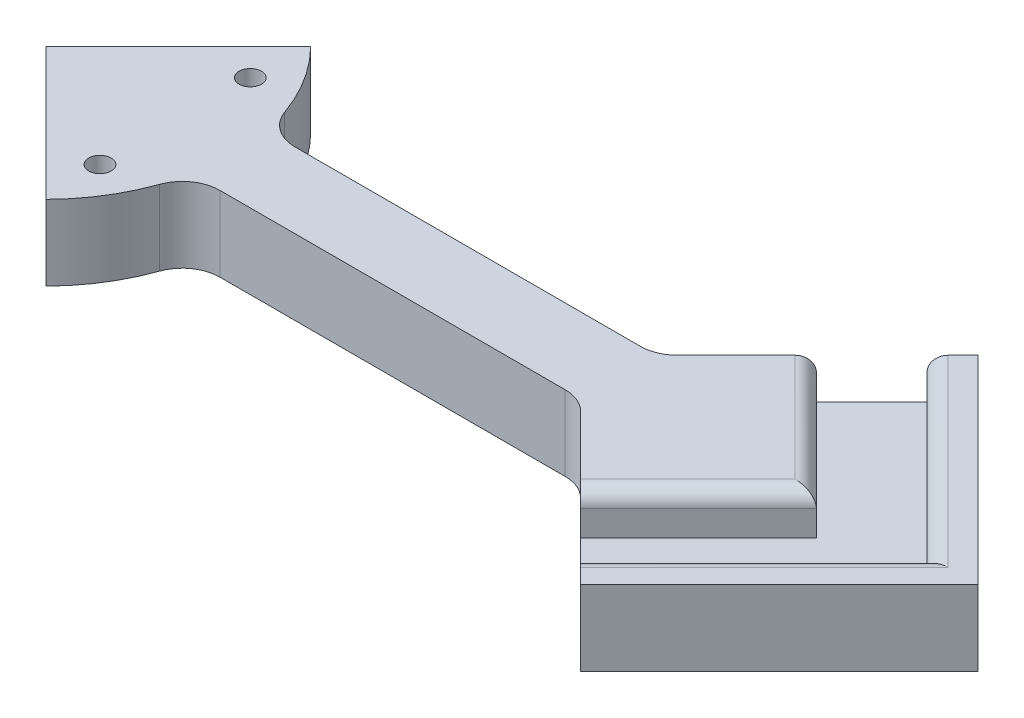
SolidWorks part; units mm, degrees
ref_plane "Front Plane" through (0, 0, 0) normal (0, 0, 1) x (1, 0, 0)
ref_plane "Top Plane" through (0, 0, 0) normal (0, 1, 0) x (1, 0, 0)
ref_plane "Right Plane" through (0, 0, 0) normal (1, 0, 0) x (0, 0, -1)
sketch "Sketch5" plane through (0, 0, 0) normal (0, 1, 0) x (1, 0, 0)
  line L0 (193.4968, 0) -> (0, 0) construction
  line L1 (0, 0) -> (69.85, 69.85) construction
  circle A0 centre (0, 0) radius 162.2828 construction
  circle A1 centre (69.85, 69.85) radius 63.5 construction
  circle A2 centre (69.85, -69.85) radius 63.5 construction
  circle A3 centre (-69.85, -69.85) radius 63.5 construction
  circle A4 centre (-69.85, 69.85) radius 63.5 construction
  point P15 (0, 0)
  dimension "D1" = 324.5656
  dimension "D2" = 127
  dimension "D3" = 45
  dimension "D4" = 4
sketch "Sketch8" plane through (0, 0, 0) normal (0, 0, 1) x (1, 0, 0)
  line L0 (0, 34.2637) -> (0, -61.9336) construction
sketch "Sketch11" plane through (0, 0, 0) normal (0, 1, 0) x (1, 0, 0)
  line L0 (0, 137.9723) -> (0, -128.7054) construction
  line L1 (-137.9723, 0) -> (137.9723, 0) construction
  line L2 (0, 0) -> (88.3597, 88.3597) construction
  dimension "D1" = 45
sketch "Sketch12" plane through (0, 0, 0) normal (0, 1, 0) x (1, 0, 0)
  line L0 (193.4968, 0) -> (0, 0) construction
  line L3 (139.8796, 6.35) -> (6.5296, 6.35)
  line L4 (6.5296, 6.35) -> (0.1796, 0)
  line L5 (0.1796, 0) -> (6.5296, -6.35)
  line L6 (6.5296, -6.35) -> (139.8796, -6.35)
  line L7 (139.8796, -6.35) -> (139.8796, 6.35)
  line L8 (0, 0) -> (69.85, 69.85) construction
  circle A28 centre (69.85, 69.85) radius 63.5 construction
  circle A33 centre (69.85, -69.85) radius 63.5 construction
  point P11 (0, 0)
  point P13 (0, 0)
  point P14 (0, 0)
  point P16 (0, 0)
  point P19 (0, 0)
  point P20 (0, 0)
  dimension "D2" = 4
  dimension "D1" = 0.127
  dimension "D5" = 133.35
extrude "Boss-Extrude11" add sketch "Sketch12" along normal blind 12.7
sketch "Sketch23" plane through (0, 0, 0) normal (0, 1, 0) x (1, 0, 0)
  line L0 (69.85, 69.85) -> (139.7, 0) construction
  line L1 (193.4968, 0) -> (0, 0) construction
  line L2 (90.521, 0) -> (124.0907, 33.5698)
  line L3 (157.6605, 0) -> (124.0907, -33.5698)
  line L4 (124.0907, -33.5698) -> (90.521, 0)
  line L5 (124.0907, 33.5698) -> (157.6605, 0)
  line L7 (0, 0) -> (69.85, 69.85) construction
  dimension "D1" = 12.7
  dimension "D2" = 64.008
extrude "Boss-Extrude12" add sketch "Sketch23" along normal up to surface (12.7 mm away) up to face at (58.5996, 12.7, 0)
sketch "Sketch26" plane through (0, 0, 0) normal (0, 1, 0) x (1, 0, 0)
  line L0 (22.5403, 22.3607) -> (0.1796, 0)
  line L1 (193.4968, 0) -> (0, 0) construction
  line L2 (0.1796, 0) -> (22.5403, -22.3607)
  line L3 (0, 0) -> (69.85, 69.85) construction
  line L4 (6.5296, 6.35) -> (0.1796, 0) construction
  arc A0 (22.5403, -22.3607) -> (22.5403, 22.3607) centre (0, 0) ccw
  dimension "D1" = 63.5
extrude "Boss-Extrude13" add sketch "Sketch26" along normal up to surface (12.7 mm away) up to face at (76.6028, 12.7, 0)
sketch "Sketch24" plane through (0, 0, 0) normal (0, 1, 0) x (1, 0, 0)
  line L0 (119.7802, 29.2592) -> (149.0395, 0)
  line L1 (124.0907, 33.5698) -> (96.871, 6.35) construction
  line L2 (193.4968, 0) -> (0, 0) construction
  line L3 (149.0395, 0) -> (119.7802, -29.2592)
  line L4 (96.871, -6.35) -> (124.0907, -33.5698) construction
  line L5 (119.7802, -29.2592) -> (110.4408, -19.9198)
  line L6 (110.4408, -19.9198) -> (130.3605, 0)
  line L7 (130.3605, 0) -> (110.4408, 19.9198)
  line L8 (110.4408, 19.9198) -> (119.7802, 29.2592)
  line L11 (115.1105, 24.5895) -> (144.3697, -4.6697) construction
  line L12 (157.6605, 0) -> (124.0907, 33.5698) construction
  dimension "D1" = 12.7
  dimension "D2" = 13.208
extrude "Cut-Extrude1" cut sketch "Sketch24" against normal blind 6.858 from surface at 12.7 starting at face at (70.9399, 12.7, 0)
sketch "Sketch25" plane through (0, 0, 0) normal (0, 1, 0) x (1, 0, 0)
  line L0 (193.4968, 0) -> (0, 0) construction
  line L1 (0, 0) -> (21.997, 12.7) construction
  line L2 (0, 0) -> (58.3902, 0) construction
  circle A1 centre (21.997, 12.7) radius 1.9
  circle A2 centre (21.997, -12.7) radius 1.9
  dimension "D1" = 3.8
  dimension "D4" = 25.4
  dimension "D5" = 30
extrude "Cut-Extrude2" cut sketch "Sketch25" along normal through all
fillet "Fillet1" radius 2.54 4 edges at (120.4006, 12.7, 9.9599) (120.4006, 12.7, -9.9599) (134.4098, 12.7, -14.6296) (134.4098, 12.7, 14.6296)
fillet "Fillet2" radius 6.35 4 edges at (96.871, 6.35, -6.35) (96.871, 6.35, 6.35) (31.1085, 6.35, -6.35) (31.1085, 6.35, 6.35)
equation "\"cage spacing\"= 0.5'space between cages"
equation "\"cage diameter\"= 5'cage diameter"
equation "\"cage radius\"= \"cage diameter\" / 2'cage radius"
equation "\"D1@Sketch5\"=2*(2^0.5*(\"cage radius\"+\"cage spacing\"/2)+\"cage radius\")"
equation "\"tightTol\"= 0.005in"
equation "\"normTol\"= 0.01in"
equation "\"looseTol\"= 0.02in"
equation "\"D2@Sketch5\"=\"cage diameter\""
equation "\"D2@Sketch23\"=\"cage radius\"+\"looseTol\""
equation "\"D2@Sketch24\"=\"looseTol\"+0.5"
equation "\"D1@Cut-Extrude1\"=\"looseTol\"+0.25"
equation "\"D1@Sketch25\"=3.8mm"
